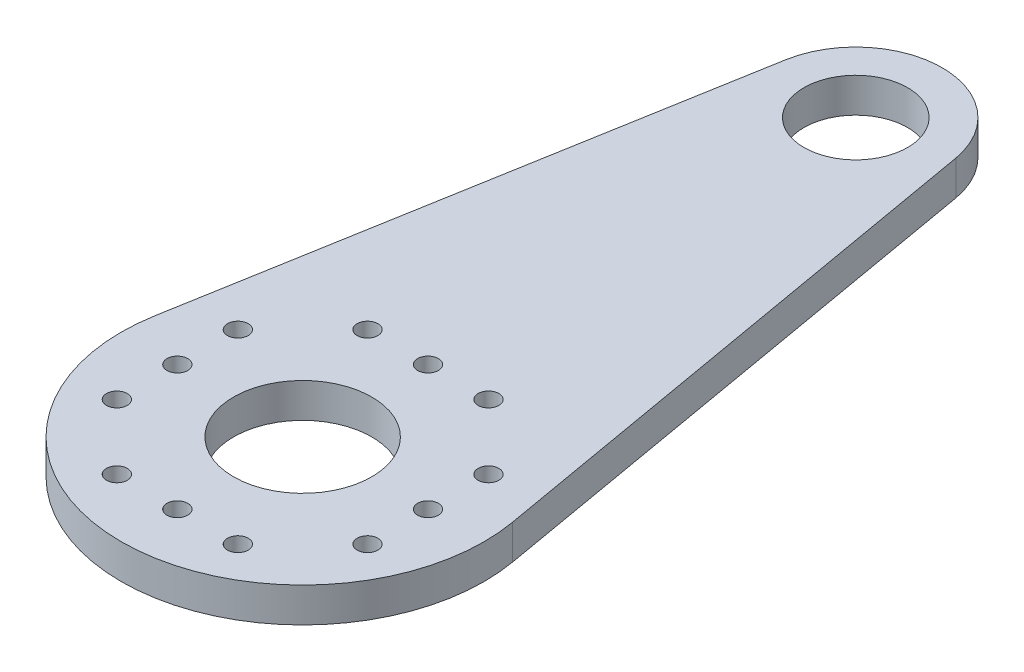
SolidWorks part; units mm, degrees
ref_plane "Alzado" through (0, 0, 0) normal (0, 0, 1) x (1, 0, 0)
ref_plane "Planta" through (0, 0, 0) normal (0, 1, 0) x (1, 0, 0)
ref_plane "Vista lateral" through (0, 0, 0) normal (1, 0, 0) x (0, 0, -1)
sketch "Croquis1" plane through (0, 0, 0) normal (0, 1, 0) x (1, 0, 0)
  line L0 (0, 0) -> (0, 32) construction
  line L1 (4.9256, 32.8594) -> (10.3437, 1.8047)
  line L2 (-4.9256, 32.8594) -> (-10.3437, 1.8047)
  arc A0 (-10.3437, 1.8047) -> (10.3437, 1.8047) centre (0, 0) ccw
  circle A1 centre (0, 0) radius 4
  circle A2 centre (0, 32) radius 3
  arc A3 (4.9256, 32.8594) -> (-4.9256, 32.8594) centre (0, 32) ccw
  dimension "D1" = 21
  dimension "D2" = 8
  dimension "D4" = 6
  dimension "D5" = 10
  dimension "D3" = 32
extrude "Saliente-Extruir1" add sketch "Croquis1" along normal blind 2
sketch "Sketch1" plane through (0, 2, 0) normal (0, 1, 0) x (1, 0, 0)
  line L0 (0, 7.25) -> (3.5, 7.25) construction
  line L1 (0, 7.25) -> (-3.5, 7.25) construction
  circle A0 centre (0, 0) radius 7.25 construction
  circle A1 centre (0, 7.25) radius 0.6
  circle A2 centre (-3.5, 7.25) radius 0.6
  circle A3 centre (3.5, 7.25) radius 0.6
  dimension "D1" = 14.5
  dimension "D2" = 1.2
  dimension "D5" = 1.2
  dimension "D6" = 1.2
  dimension "D3" = 3.5
  dimension "D4" = 3.5
extrude "Cut-Extrude1" cut sketch "Sketch1" against normal up to surface (2 mm away) up to face at (0, 0, -15.291)
pattern_circular "CirPattern1" count 4 over 360 about axis through (0, 0, 0) along (0, 1, 0) of "Cut-Extrude1"
